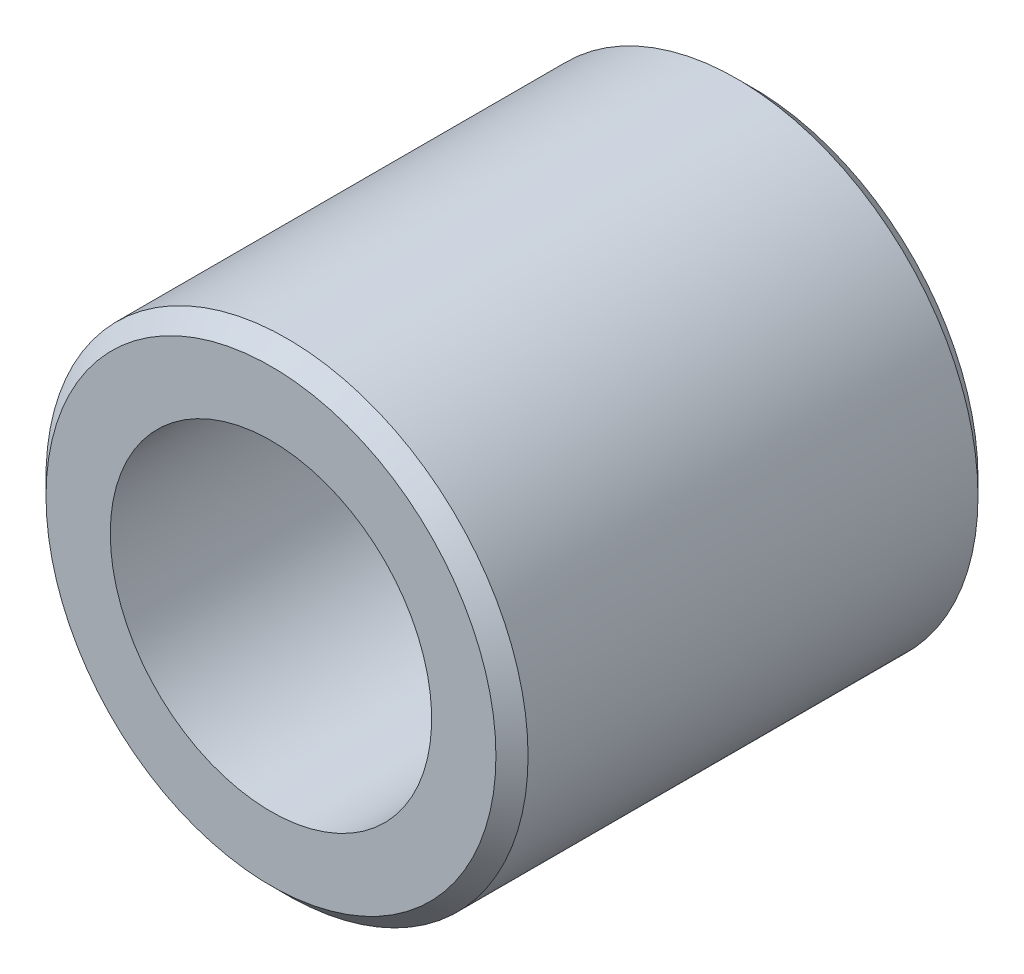
SolidWorks part; units mm, degrees
ref_plane "Ön Düzlem" through (0, 0, 0) normal (0, 0, 1) x (1, 0, 0)
ref_plane "Üst Düzlem" through (0, 0, 0) normal (0, 1, 0) x (1, 0, 0)
ref_plane "Sağ Düzlem" through (0, 0, 0) normal (1, 0, 0) x (0, 0, -1)
sketch "Çizim1" plane through (0, 0, 0) normal (0, 0, 1) x (1, 0, 0)
  circle A0 centre (0, 0) radius 15
  dimension "D1" = 30
extrude "Yükseklik-Ekstrüzyon1" add sketch "Çizim1" along normal blind 30
sketch "Çizim2" plane through (0, 0, 0) normal (0, 0, -1) x (-1, 0, 0)
  circle A0 centre (0, 0) radius 10
  dimension "D1" = 20
extrude "Kes-Ekstrüzyon1" cut sketch "Çizim2" against normal through all
chamfer "Pah1" distance 1 angle 45 2 edges at (15, 0, 30) (15, 0, 0)
